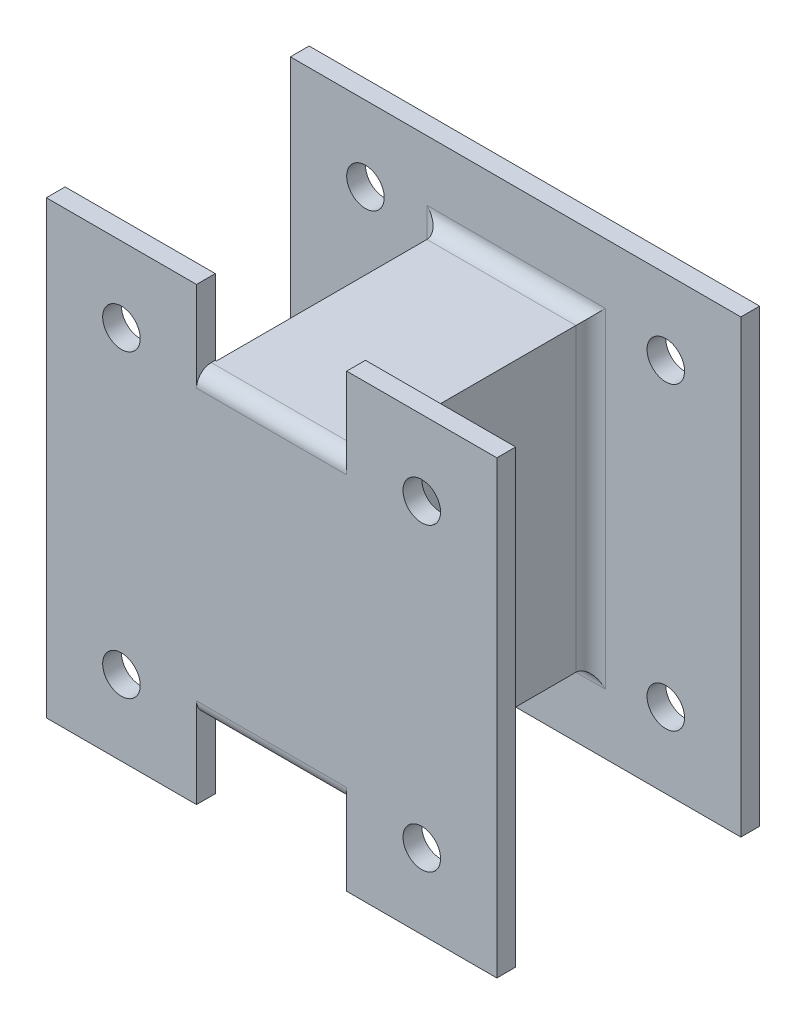
SolidWorks part; units mm, degrees
material "Plain Carbon Steel"
ref_plane "Front Plane" through (0, 0, 0) normal (0, 0, 1) x (1, 0, 0)
ref_plane "Top Plane" through (0, 0, 0) normal (0, 1, 0) x (1, 0, 0)
ref_plane "Right Plane" through (0, 0, 0) normal (1, 0, 0) x (0, 0, -1)
sketch "Sketch1" plane through (0, 0, 0) normal (0, 0, 1) x (1, 0, 0)
  line L1 (0, 0) -> (152.4, 0)
  line L2 (0, 0) -> (0, 152.4)
  line L3 (0, 152.4) -> (152.4, 152.4)
  line L4 (152.4, 0) -> (152.4, 152.4)
  circle A0 centre (25.4, 127) radius 6.35
  circle A1 centre (127, 127) radius 6.35
  circle A2 centre (127, 25.4) radius 6.35
  circle A3 centre (25.4, 25.4) radius 6.35
  dimension "D3" = 12.7
  dimension "D4" = 25.4
  dimension "D1" = 152.4
  dimension "D2" = 152.4
  dimension "D5" = 25.4
  dimension "D6" = 2
  dimension "D7" = 2
extrude "Boss-Extrude1" add sketch "Sketch1" along normal blind 6.35
sketch "Sketch2" plane through (0, 0, 6.35) normal (0, 0, 1) x (1, 0, 0)
  line L0 (152.4, 152.4) -> (0, 152.4) construction
  line L1 (51.2, 127) -> (101.6, 127)
  line L2 (51.2, 127) -> (51.2, 25.4)
  line L3 (51.2, 25.4) -> (101.6, 25.4)
  line L4 (101.6, 127) -> (101.6, 25.4)
  line L5 (0, 0) -> (152.4, 0) construction
  line L6 (152.4, 0) -> (152.4, 152.4) construction
  dimension "D1" = 50.4
  dimension "D2" = 25.4
  dimension "D3" = 25.4
  dimension "D4" = 50.8
extrude "Boss-Extrude2" add sketch "Sketch2" along normal blind 76.2 contours L2 L1 L4 L3
sketch "Sketch3" plane through (0, 0, 82.55) normal (0, 0, 1) x (1, 0, 0)
  line L0 (101.6, 152.4) -> (152.4, 152.4)
  line L1 (0, 152.4) -> (50.8, 152.4)
  line L2 (0, 152.4) -> (0, 0)
  line L3 (0, 0) -> (50.8, 0)
  line L4 (152.4, 152.4) -> (152.4, 0)
  line L6 (50.8, 152.4) -> (50.8, 127)
  line L7 (50.8, 127) -> (101.6, 127)
  line L8 (101.6, 152.4) -> (101.6, 127)
  line L9 (0, 76.2) -> (152.4, 76.2) construction
  line L11 (101.6, 0) -> (101.6, 25.4)
  line L12 (50.8, 25.4) -> (101.6, 25.4)
  line L13 (50.8, 0) -> (50.8, 25.4)
  line L14 (101.6, 0) -> (152.4, 0)
  circle A0 centre (25.4, 127) radius 6.35
  circle A1 centre (127, 127) radius 6.35
  circle A2 centre (127, 25.4) radius 6.35
  circle A3 centre (25.4, 25.4) radius 6.35
  dimension "D1" = 12.7
  dimension "D2" = 2
  dimension "D4" = 50.8
  dimension "D3" = 2
extrude "Boss-Extrude3" add sketch "Sketch3" along normal blind 6.35
fillet "Fillet2" radius 5 4 edges at (51.2, 76.2, 6.35) (76.4, 25.4, 6.35) (101.6, 76.2, 6.35) (76.4, 127, 6.35)
fillet "Fillet6" radius 5 2 edges at (76.2, 25.4, 88.9) (76.2, 127, 88.9)
